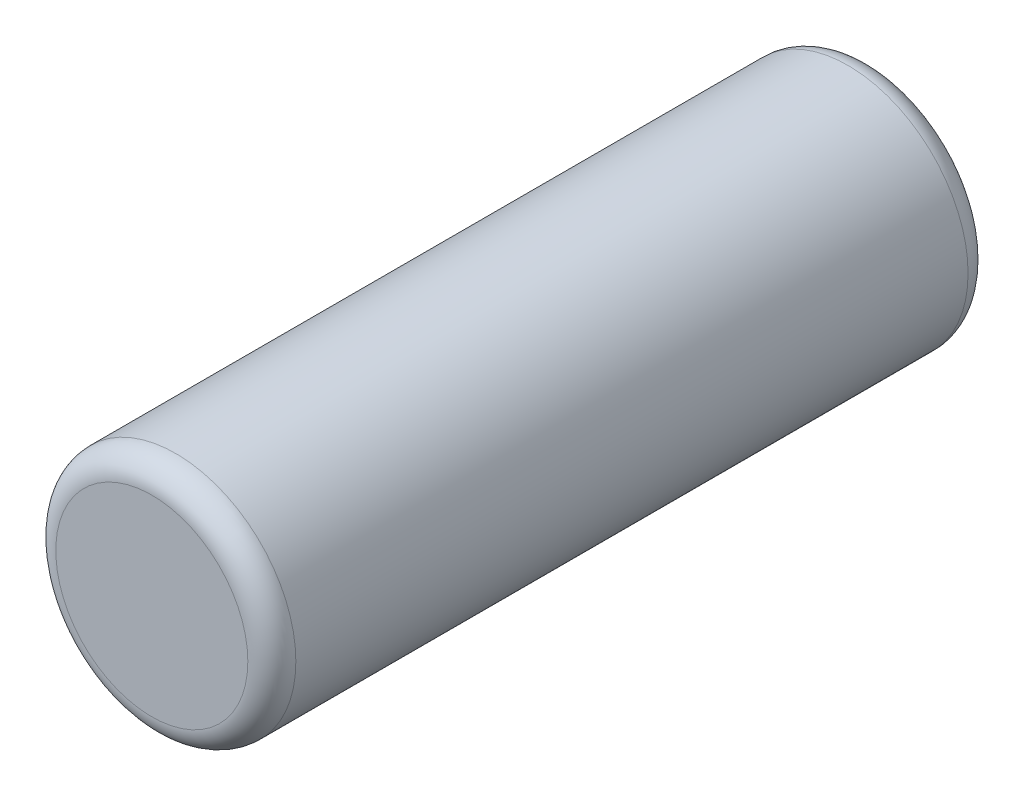
SolidWorks part; units mm, degrees
ref_plane "Front" through (0, 0, 0) normal (0, 0, 1) x (1, 0, 0)
ref_plane "Top" through (0, 0, 0) normal (0, 1, 0) x (1, 0, 0)
ref_plane "Right" through (0, 0, 0) normal (1, 0, 0) x (0, 0, -1)
sketch "Sketch1" plane through (0, 0, 0) normal (0, 0, 1) x (1, 0, 0)
  circle A0 centre (0, 0) radius 2.5
  dimension "D1" = 5
extrude "Boss-Extrude1" add sketch "Sketch1" along normal blind 15
fillet "Fillet1" radius 0.5 2 edges at (2.5, 0, 0) (2.5, 0, 15)
